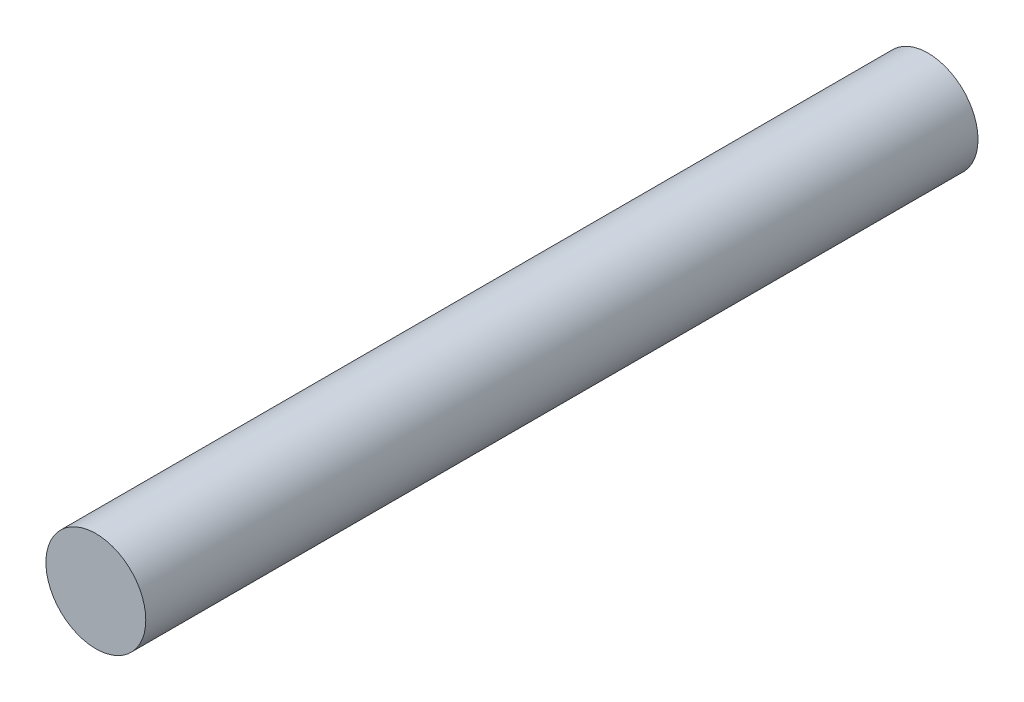
SolidWorks part; units mm, degrees
ref_plane "Front Plane" through (0, 0, 0) normal (0, 0, 1) x (1, 0, 0)
ref_plane "Top Plane" through (0, 0, 0) normal (0, 1, 0) x (1, 0, 0)
ref_plane "Right Plane" through (0, 0, 0) normal (1, 0, 0) x (0, 0, -1)
sketch "Sketch1" plane through (0, 0, 0) normal (0, 0, 1) x (1, 0, 0)
  circle A0 centre (0, 0) radius 1.5
  dimension "D1" = 3
extrude "Boss-Extrude1" add sketch "Sketch1" against normal blind 25
